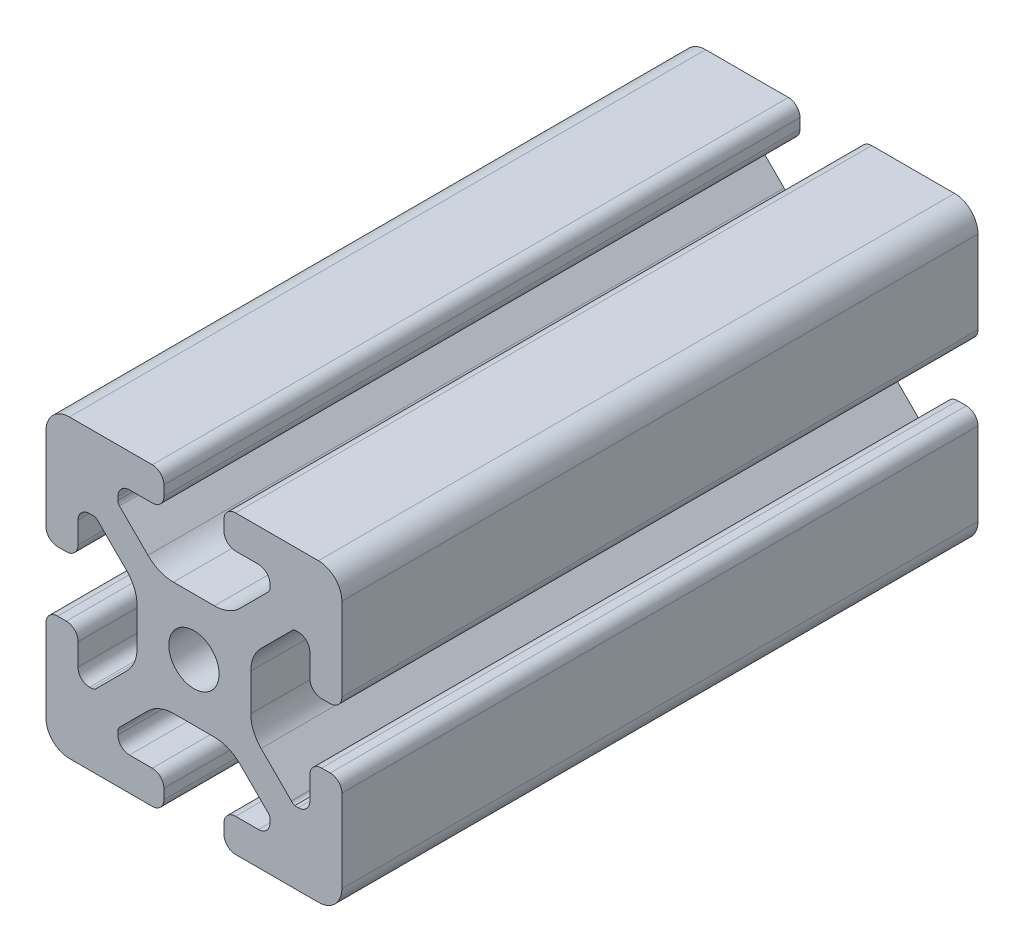
SolidWorks part; units mm, degrees
material "6105-T5 Aluminum"
ref_plane "Front Plane" through (0, 0, 0) normal (0, 0, 1) x (1, 0, 0)
ref_plane "Top Plane" through (0, 0, 0) normal (0, 1, 0) x (1, 0, 0)
ref_plane "Right Plane" through (0, 0, 0) normal (1, 0, 0) x (0, 0, -1)
sketch "Sketch1" plane through (0, 0, 0) normal (0, 0, 1) x (1, 0, 0)
  line L0 (0, 19.7407) -> (0, -19.7407) construction
  line L1 (19.0335, 0) -> (-20.7246, 0) construction
  line L2 (-8.715, -15.5246) -> (-5.63, -15.5246)
  line L3 (-10.285, -13.9546) -> (-10.285, -13.4925)
  line L4 (-6.2171, -9.1098) -> (-10.0624, -12.9551)
  line L5 (2.7773, -7.685) -> (-2.7773, -7.685)
  line L6 (10.0624, -12.9551) -> (6.2171, -9.1098)
  line L7 (10.285, -13.9546) -> (10.285, -13.4925)
  line L8 (5.63, -15.5246) -> (8.715, -15.5246)
  line L9 (4.06, -18.43) -> (4.06, -17.0946)
  line L10 (-4.06, -18.43) -> (-4.06, -17.0946)
  line L11 (15.68, -8.7154) -> (15.68, -5.63)
  line L12 (-14.11, -10.2854) -> (-13.8169, -10.2854)
  line L13 (20, -16.83) -> (20, -5.63)
  line L14 (20, 5.63) -> (20, 13.0011)
  line L15 (-16.83, 20) -> (-5.63, 20)
  line L16 (5.63, 20) -> (12.9796, 20)
  line L18 (-8.715, 15.5246) -> (-5.63, 15.5246)
  line L19 (-20, -17.0184) -> (-20, -5.7579)
  line L20 (-20, 5.573) -> (-20, 13.0045)
  line L21 (-15.68, -8.7154) -> (-15.68, -5.7579)
  line L23 (-16.6746, -20) -> (-5.63, -20)
  line L24 (5.63, -20) -> (13, -20)
  line L53 (14.11, -10.2854) -> (13.6201, -10.2854)
  line L54 (13.1637, -9.947) -> (9.0762, -5.8595)
  line L55 (7.685, -2.5008) -> (7.685, 2.5008)
  line L56 (9.0762, 5.8595) -> (13.2795, 10.0628)
  line L57 (13.8169, 10.2854) -> (14.11, 10.2854)
  line L58 (15.68, 8.7154) -> (15.68, 5.63)
  line L59 (17.25, 4.06) -> (18.43, 4.06)
  line L61 (20, 13.0011) -> (20, 16.83)
  line L62 (16.83, 20) -> (12.9796, 20)
  line L64 (4.06, 18.43) -> (4.06, 17.0946)
  line L65 (5.63, 15.5246) -> (8.715, 15.5246)
  line L66 (10.285, 13.9546) -> (10.285, 13.4925)
  line L67 (10.0624, 12.9551) -> (6.2171, 9.1098)
  line L68 (2.7773, 7.685) -> (-2.7773, 7.685)
  line L69 (-6.2171, 9.1098) -> (-10.0624, 12.9551)
  line L70 (-10.285, 13.4925) -> (-10.285, 13.9546)
  line L72 (-4.06, 17.0946) -> (-4.06, 18.43)
  line L75 (-20, 16.83) -> (-20, 13.0045)
  line L77 (-18.43, 4.003) -> (-17.25, 4.003)
  line L78 (-15.68, 5.573) -> (-15.68, 8.4757)
  line L79 (-14.0552, 10.0447) -> (-13.7199, 10.033)
  line L80 (-13.0405, 9.8238) -> (-9.0762, 5.8595)
  line L81 (-7.685, 2.5008) -> (-7.685, -2.5008)
  line L82 (-9.0762, -5.8595) -> (-13.2795, -10.0628)
  line L85 (-17.25, -4.1204) -> (-18.43, -4.1204)
  line L100 (13, -20) -> (16.83, -20)
  line L103 (18.43, -4.06) -> (17.25, -4.06)
  arc A0 (-5.63, -15.5246) -> (-4.06, -17.0946) centre (-5.63, -17.0946) cw
  arc A1 (-8.715, -15.5246) -> (-10.285, -13.9546) centre (-8.715, -13.9546) cw
  arc A2 (-10.285, -13.4925) -> (-10.0624, -12.9551) centre (-9.525, -13.4925) cw
  arc A3 (-6.2171, -9.1098) -> (-2.7773, -7.685) centre (-2.7773, -12.5496) cw
  arc A4 (2.7773, -7.685) -> (6.2171, -9.1098) centre (2.7773, -12.5496) cw
  arc A5 (10.0624, -12.9551) -> (10.285, -13.4925) centre (9.525, -13.4925) cw
  arc A6 (10.285, -13.9546) -> (8.715, -15.5246) centre (8.715, -13.9546) cw
  arc A7 (4.06, -17.0946) -> (5.63, -15.5246) centre (5.63, -17.0946) cw
  arc A8 (5.63, -20) -> (4.06, -18.43) centre (5.63, -18.43) cw
  arc A9 (-4.06, -18.43) -> (-5.63, -20) centre (-5.63, -18.43) cw
  circle A45 centre (0, 0) radius 3.4
  arc A46 (17.25, -4.06) -> (15.68, -5.63) centre (17.25, -5.63) ccw
  arc A47 (14.11, -10.2854) -> (15.68, -8.7154) centre (14.11, -8.7154) ccw
  arc A48 (13.1637, -9.947) -> (13.6201, -10.2854) centre (13.8117, -9.55) ccw
  arc A49 (7.685, -2.5008) -> (9.0762, -5.8595) centre (12.435, -2.5008) ccw
  arc A50 (9.0762, 5.8595) -> (7.685, 2.5008) centre (12.435, 2.5008) ccw
  arc A51 (13.8169, 10.2854) -> (13.2795, 10.0628) centre (13.8169, 9.5254) ccw
  arc A52 (15.68, 8.7154) -> (14.11, 10.2854) centre (14.11, 8.7154) ccw
  arc A53 (15.68, 5.63) -> (17.25, 4.06) centre (17.25, 5.63) ccw
  arc A54 (18.43, 4.06) -> (20, 5.63) centre (18.43, 5.63) ccw
  arc A55 (20, 16.83) -> (16.83, 20) centre (16.83, 16.83) ccw
  arc A56 (5.63, 20) -> (4.06, 18.43) centre (5.63, 18.43) ccw
  arc A57 (4.06, 17.0946) -> (5.63, 15.5246) centre (5.63, 17.0946) ccw
  arc A58 (10.285, 13.9546) -> (8.715, 15.5246) centre (8.715, 13.9546) ccw
  arc A59 (10.0624, 12.9551) -> (10.285, 13.4925) centre (9.525, 13.4925) ccw
  arc A60 (2.7773, 7.685) -> (6.2171, 9.1098) centre (2.7773, 12.5496) ccw
  arc A61 (-6.2171, 9.1098) -> (-2.7773, 7.685) centre (-2.7773, 12.5496) ccw
  arc A62 (-10.285, 13.4925) -> (-10.0624, 12.9551) centre (-9.525, 13.4925) ccw
  arc A63 (-8.715, 15.5246) -> (-10.285, 13.9546) centre (-8.715, 13.9546) ccw
  arc A64 (-5.63, 15.5246) -> (-4.06, 17.0946) centre (-5.63, 17.0946) ccw
  arc A65 (-4.06, 18.43) -> (-5.63, 20) centre (-5.63, 18.43) ccw
  arc A66 (-16.83, 20) -> (-20, 16.83) centre (-16.83, 16.83) ccw
  arc A67 (-20, 5.573) -> (-18.43, 4.003) centre (-18.43, 5.573) ccw
  arc A68 (-17.25, 4.003) -> (-15.68, 5.573) centre (-17.25, 5.573) ccw
  arc A69 (-14.0552, 10.0447) -> (-15.68, 8.4757) centre (-14.11, 8.4757) ccw
  arc A70 (-13.0405, 9.8238) -> (-13.7199, 10.033) centre (-13.5779, 9.2864) ccw
  arc A71 (-7.685, 2.5008) -> (-9.0762, 5.8595) centre (-12.435, 2.5008) ccw
  arc A72 (-9.0762, -5.8595) -> (-7.685, -2.5008) centre (-12.435, -2.5008) ccw
  arc A73 (-13.8169, -10.2854) -> (-13.2795, -10.0628) centre (-13.8169, -9.5254) ccw
  arc A74 (-15.68, -8.7154) -> (-14.11, -10.2854) centre (-14.11, -8.7154) ccw
  arc A75 (-15.68, -5.7579) -> (-17.25, -4.1204) centre (-17.2485, -5.6904) ccw
  arc A76 (-18.43, -4.1204) -> (-20, -5.7579) centre (-18.4315, -5.6904) ccw
  arc A77 (-20, -17.0184) -> (-16.6746, -20) centre (-16.8354, -16.8341) ccw
  arc A88 (16.83, -20) -> (20, -16.83) centre (16.83, -16.83) ccw
  arc A89 (20, -5.63) -> (18.43, -4.06) centre (18.43, -5.63) ccw
  dimension "D2" = 6.8
  dimension "D7" = 20.57
  dimension "D1" = 40
  dimension "D3" = 4.32
  dimension "D4" = 15.37
  dimension "D5" = 20
  dimension "D6" = 4.32
  dimension "D9" = 15.37
extrude "Extrude1" add sketch "Sketch1" against normal blind 86
